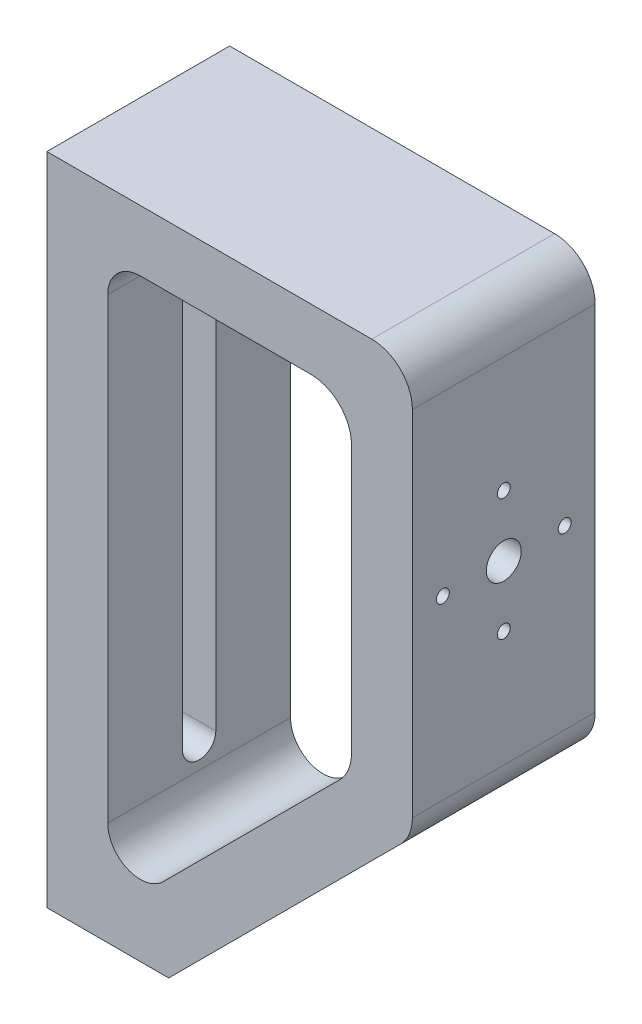
SolidWorks part; units mm, degrees
ref_plane "Front Plane" through (0, 0, 0) normal (0, 0, 1) x (1, 0, 0)
ref_plane "Top Plane" through (0, 0, 0) normal (0, 1, 0) x (1, 0, 0)
ref_plane "Right Plane" through (0, 0, 0) normal (1, 0, 0) x (0, 0, -1)
sketch "Sketch1" plane through (0, 0, 0) normal (0, 0, 1) x (1, 0, 0)
  line L0 (0, 0) -> (0, 191.2132)
  line L1 (0, 191.2132) -> (80, 191.2132)
  line L2 (90, 181.2132) -> (90, 94.1421)
  line L3 (87.0711, 87.0711) -> (0, 0)
  line L4 (72.0711, 93.2843) -> (28.6569, 49.8701)
  line L5 (15, 55.5269) -> (15, 168.2132)
  line L6 (23, 176.2132) -> (65, 176.2132)
  line L7 (75, 166.2132) -> (75, 100.3553)
  line L8 (15, 176.2132) -> (75, 176.2132) construction
  line L9 (75, 176.2132) -> (75, 96.2132) construction
  line L10 (75, 96.2132) -> (15, 36.2132) construction
  line L11 (90, 90) -> (0, 0) construction
  line L12 (90, 191.2132) -> (90, 90) construction
  line L13 (0, 191.2132) -> (90, 191.2132) construction
  line L14 (15, 36.2132) -> (15, 176.2132) construction
  arc A0 (65, 176.2132) -> (75, 166.2132) centre (65, 166.2132) cw
  arc A1 (75, 100.3553) -> (72.0711, 93.2843) centre (65, 100.3553) cw
  arc A2 (87.0711, 87.0711) -> (90, 94.1421) centre (80, 94.1421) ccw
  arc A3 (90, 181.2132) -> (80, 191.2132) centre (80, 181.2132) ccw
  arc A4 (15, 55.5269) -> (28.6569, 49.8701) centre (23, 55.5269) ccw
  arc A5 (15, 168.2132) -> (23, 176.2132) centre (23, 168.2132) cw
  point P12 (75, 176.2132)
  dimension "D5" = 10
  dimension "D2" = 8
  dimension "D3" = 135
  dimension "D4" = 90
  dimension "D1" = 15
extrude "Body" add sketch "Sketch1" along normal blind 45
chamfer "Bottom Trim" distance 30 angle 90 1 edges at (0, 0, 22.5)
sketch "Sketch2" plane through (90, 0, 0) normal (1, 0, 0) x (0, 0, -1)
  line L0 (-45, 181.2132) -> (0, 94.1421) construction
  line L1 (0, 181.2132) -> (-45, 94.1421) construction
  line L2 (-22.5, 137.6777) -> (-22.5, 152.6777) construction
  circle A0 centre (-22.5, 137.6777) radius 4.3
  circle A1 centre (-22.5, 137.6777) radius 15 construction
  circle A2 centre (-22.5, 152.6777) radius 1.6
  circle A3 centre (-7.5, 137.6777) radius 1.6
  circle A4 centre (-22.5, 122.6777) radius 1.6
  circle A5 centre (-37.5, 137.6777) radius 1.6
  point P13 (-40.6933, 138.991)
  point P14 (0, 0)
  point P22 (-22.5, 137.6777)
  dimension "D1" = 8.6
  dimension "D2" = 30
  dimension "D3" = 3.2
  dimension "D4" = 4
extrude "Front Mounting Holes" cut sketch "Sketch2" against normal up to next
sketch "Sketch3" plane through (75, 0, 0) normal (-1, 0, 0) x (0, 0, 1)
  line L0 (40.35, 136.0322) -> (40.35, 139.3231)
  line L1 (24.1454, 155.5277) -> (20.8546, 155.5277)
  line L2 (20.8546, 155.5277) -> (19.2091, 152.6777)
  line L3 (19.2091, 152.6777) -> (20.8546, 149.8277)
  line L4 (20.8546, 149.8277) -> (24.1454, 149.8277)
  line L5 (24.1454, 149.8277) -> (25.7909, 152.6777)
  line L6 (25.7909, 152.6777) -> (24.1454, 155.5277)
  line L7 (40.35, 139.3231) -> (37.5, 140.9686)
  line L8 (37.5, 140.9686) -> (34.65, 139.3231)
  line L9 (34.65, 139.3231) -> (34.65, 136.0322)
  line L10 (34.65, 136.0322) -> (37.5, 134.3868)
  line L11 (37.5, 134.3868) -> (40.35, 136.0322)
  line L12 (20.8546, 119.8277) -> (24.1454, 119.8277)
  line L13 (24.1454, 119.8277) -> (25.7909, 122.6777)
  line L14 (25.7909, 122.6777) -> (24.1454, 125.5277)
  line L15 (24.1454, 125.5277) -> (20.8546, 125.5277)
  line L16 (20.8546, 125.5277) -> (19.2091, 122.6777)
  line L17 (19.2091, 122.6777) -> (20.8546, 119.8277)
  line L18 (4.65, 139.3231) -> (4.65, 136.0322)
  line L19 (4.65, 136.0322) -> (7.5, 134.3868)
  line L20 (7.5, 134.3868) -> (10.35, 136.0322)
  line L21 (10.35, 136.0322) -> (10.35, 139.3231)
  line L22 (10.35, 139.3231) -> (7.5, 140.9686)
  line L23 (7.5, 140.9686) -> (4.65, 139.3231)
  circle A0 centre (22.5, 152.6777) radius 2.85 construction
  point P11 (22.5, 137.6777)
  point P30 (22.5, 137.6777)
  dimension "D1" = 5.7
  dimension "D2" = 4
extrude "Front Mounting Holes Counterbore" cut sketch "Sketch3" against normal blind 3.5
sketch "Sketch4" plane through (0, 0, 0) normal (-1, 0, 0) x (0, 0, 1)
  line L0 (0, 168.2132) -> (45, 55.5269) construction
  line L1 (22.5, 161.8701) -> (22.5, 61.8701) construction
  line L2 (26.6, 161.8701) -> (26.6, 61.8701)
  line L3 (18.4, 161.8701) -> (18.4, 61.8701)
  arc A0 (26.6, 161.8701) -> (18.4, 161.8701) centre (22.5, 161.8701) ccw
  arc A1 (18.4, 61.8701) -> (26.6, 61.8701) centre (22.5, 61.8701) ccw
  point P6 (22.5, 111.8701)
  point P11 (0, 0)
  point P12 (0, 0)
  point P14 (0, 0)
  dimension "D2" = 4.1
  dimension "D1" = 100
extrude "Back Mounting Slot" cut sketch "Sketch4" against normal up to next
